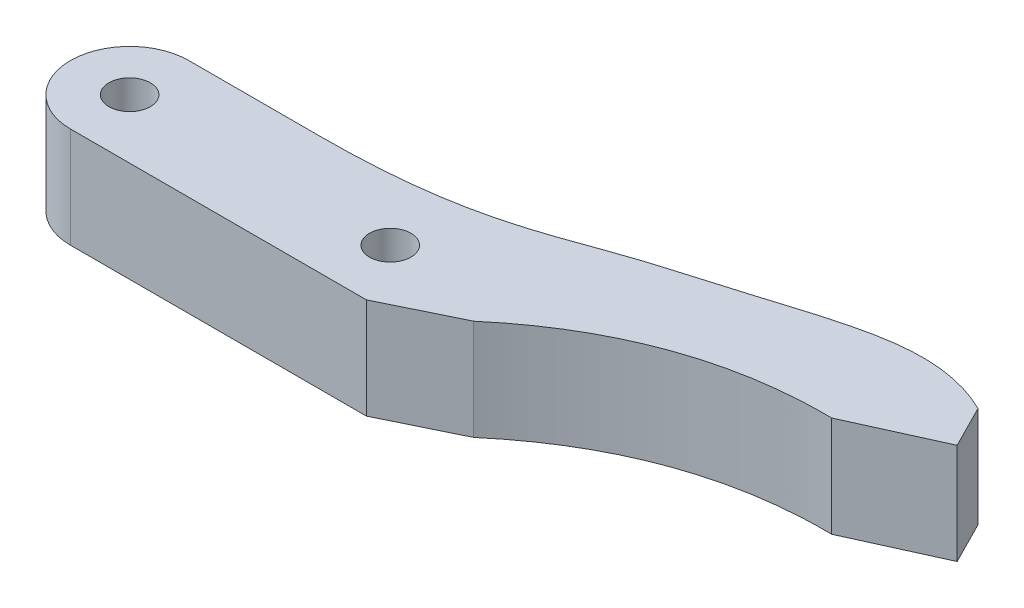
SolidWorks part; units mm, degrees
ref_plane "Front Plane" through (0, 0, 0) normal (0, 0, 1) x (1, 0, 0)
ref_plane "Top Plane" through (0, 0, 0) normal (0, 1, 0) x (1, 0, 0)
ref_plane "Right Plane" through (0, 0, 0) normal (1, 0, 0) x (0, 0, -1)
sketch "Sketch2" plane through (0, 0, 0) normal (0, 1, 0) x (1, 0, 0)
  line L1 (27, 5) -> (-5, 5)
  line L2 (27, 5) -> (27, -5)
  line L3 (27, -5) -> (-5, -5)
  line L4 (-5, 5) -> (-5, -5)
  line L5 (27, 5) -> (-5, -5) construction
  line L6 (27, -5) -> (-5, 5) construction
  circle A0 centre (0, 0) radius 1.75
  circle A1 centre (0, 0) radius 5
  circle A2 centre (22, 0) radius 1.75
  circle A3 centre (22, 0) radius 5
  point P7 (11, 0)
  dimension "D1" = 22
  dimension "D2" = 10
  dimension "D3" = 3.5
extrude "Boss-Extrude1" add sketch "Sketch2" along normal blind 8.5 contours A3 L1 A1 L3 | A1 A0 | A3 A2
sketch "Sketch3" plane through (0, 8.5, 0) normal (0, 1, 0) x (1, 0, 0)
  line L0 (22, -5) -> (24.99, -5)
  line L1 (22, -5) -> (0, -5) construction
  line L2 (24.99, -5) -> (31.08, -2.0297)
  line L3 (22, 5) -> (0, 5) construction
  line L4 (58.75, 12.87) -> (60.557, 9.3014)
  line L5 (60.557, 9.3014) -> (53.27, 6)
  line L6 (17.4898, 5) -> (4.4855, 5) construction
  line L7 (22, 5) -> (11, 5)
  circle A0 centre (22, 0) radius 1.75 construction
  arc A1 (22, -5) -> (22, 5) centre (22, 0) ccw construction
  arc A2 (22, -5) -> (22, 5) centre (22, 0) ccw
  spline S0 degree 3 poles (11, 5) (23.321, 5) (28.9604, 8.22) (46.0602, 12.9767) (52.5333, 15.9183) (58.75, 12.87) knots 0 0 0 0 0.362025 0.462025 1 1 1 1
  spline S1 degree 2 poles (31.08, -2.0297) (40.7387, 6.1883) (53.27, 6) knots 0 0 0 1 1 1
  dimension "D6" = 36.75
  dimension "D2" = 26
  dimension "D3" = 8
  dimension "D4" = 4
  dimension "D5" = 11
  dimension "D7" = 2.99
  dimension "D8" = 9.08
  dimension "D9" = 13.52
  dimension "D10" = 20.52
  dimension "D11" = 31.27
  dimension "D12" = 9.45
  dimension "D13" = 47.75
  dimension "D14" = 15.03
extrude "Boss-Extrude2" add sketch "Sketch3" against normal blind 8.5
